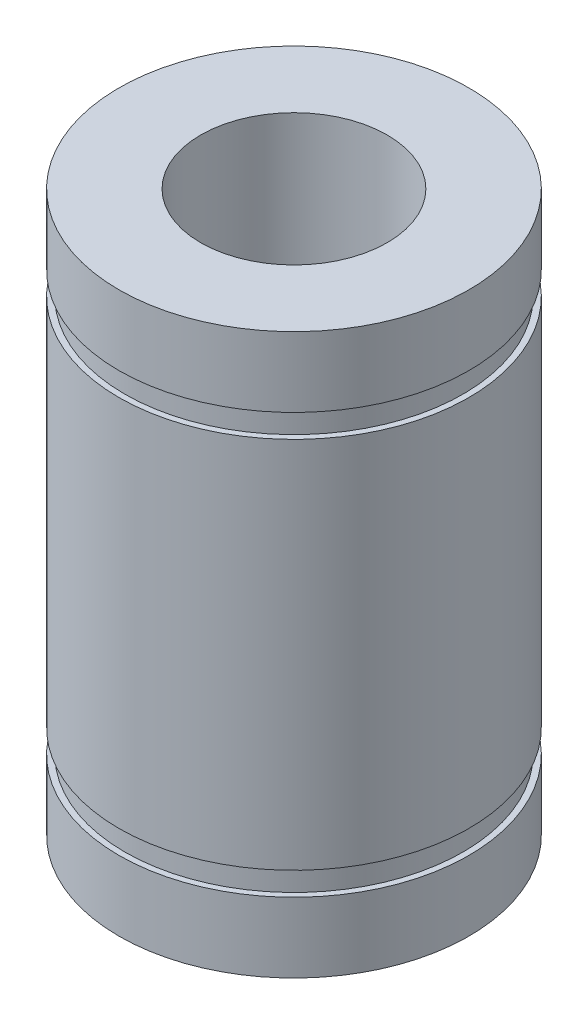
SolidWorks part; units mm, degrees
material "1.7036 (28CrS4)"
ref_plane "Plano frontal" through (0, 0, 0) normal (0, 0, 1) x (1, 0, 0)
ref_plane "Plano superior" through (0, 0, 0) normal (0, 1, 0) x (1, 0, 0)
ref_plane "Plano direito" through (0, 0, 0) normal (1, 0, 0) x (0, 0, -1)
sketch "Esboço1" plane through (0, 0, 0) normal (0, 0, 1) x (1, 0, 0)
  line L0 (4, 0) -> (7.5, 0)
  line L1 (7.5, 0) -> (7.5, -3)
  line L2 (7.5, -3) -> (7.25, -3)
  line L3 (7.25, -3) -> (7.25, -4)
  line L4 (7.25, -4) -> (7.5, -4)
  line L5 (7.5, -4) -> (7.5, -20)
  line L6 (7.5, -20) -> (7.25, -20)
  line L7 (7.25, -20) -> (7.25, -21)
  line L8 (7.25, -21) -> (7.5, -21)
  line L9 (7.5, -21) -> (7.5, -24)
  line L10 (7.5, -24) -> (4, -24)
  line L11 (4, -24) -> (4, 0)
  line L12 (0, 0) -> (0, -9.9588) construction
  point P17 (4, -12)
  point P18 (7.5, -12)
  dimension "D1" = 8
  dimension "D2" = 15
  dimension "D3" = 14.5
  dimension "D4" = 3
  dimension "D5" = 24
  dimension "D6" = 1
revolve "Revolução1" add sketch "Esboço1" angle 360 about L12
